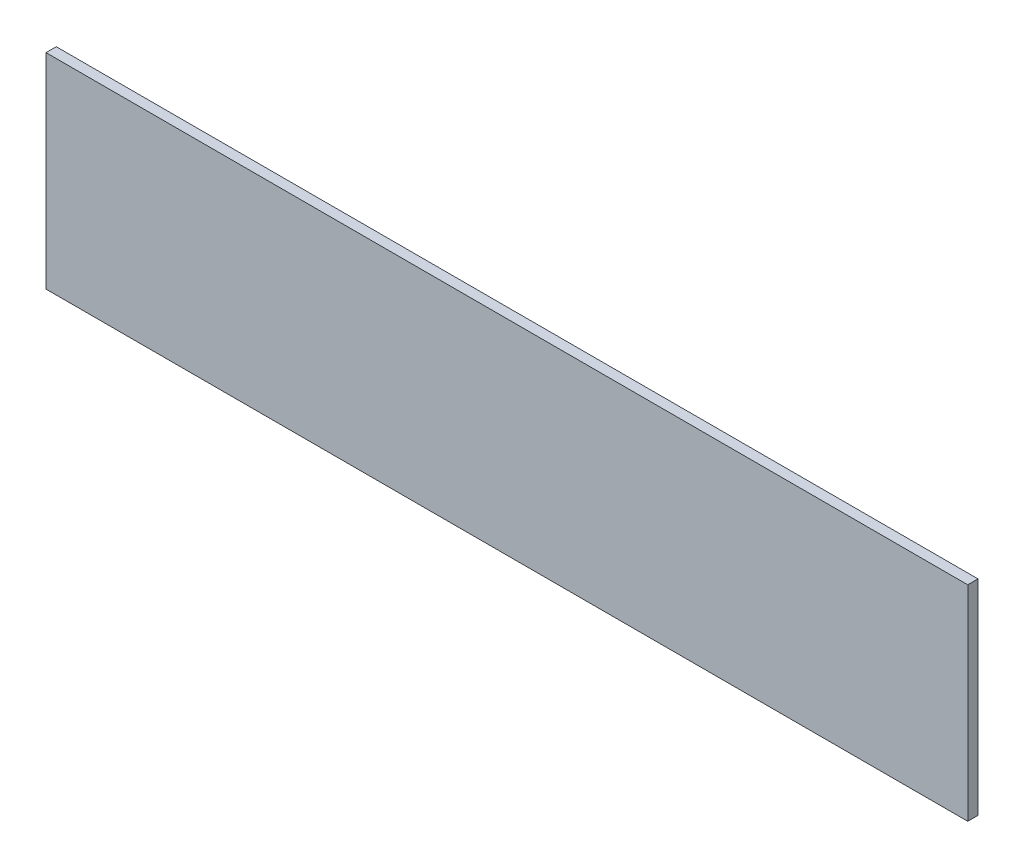
SolidWorks part; units mm, degrees
ref_plane "Plan de face" through (0, 0, 0) normal (0, 0, 1) x (1, 0, 0)
ref_plane "Plan de dessus" through (0, 0, 0) normal (0, 1, 0) x (1, 0, 0)
ref_plane "Plan de droite" through (0, 0, 0) normal (1, 0, 0) x (0, 0, -1)
sketch "Esquisse1" plane through (0, 0, 0) normal (0, 0, 1) x (1, 0, 0)
  line L1 (-235.4309, 27.7197) -> (34.5691, 27.7197)
  line L2 (-235.4309, 27.7197) -> (-235.4309, -32.2803)
  line L3 (-235.4309, -32.2803) -> (34.5691, -32.2803)
  line L4 (34.5691, 27.7197) -> (34.5691, -32.2803)
  dimension "D1" = 60
  dimension "D2" = 270
extrude "Boss.-Extru.1" add sketch "Esquisse1" along normal blind 3
equation "\"EpaisseurPlaque\"= 3"
equation "\"ProfondeurBoite\"=460"
equation "\"LongueurSyphon\"=270"
equation "\"LargeurSyphon\"=120"
equation "\"HauteurCoteDroit\"= 490"
equation "\"HauteurCoteGauche\"= 540"
equation "\"HauteurSolSyphon\"= 300"
equation "\"HauteurSyphon\"=\"HauteurCoteGauche\"-\"HauteurSolSyphon\""
equation "\"LargeurDroite\"=10"
equation "\"LargeurGauche\"=150"
equation "\"LargeurBoite\"= \"LargeurDroite\" + \"LargeurGauche\" + \"LargeurSyphon\""
equation "\"HauteurBagueSyphon\"=50"
equation "\"D2@Esquisse1\"=\"LongueurSyphon\""
